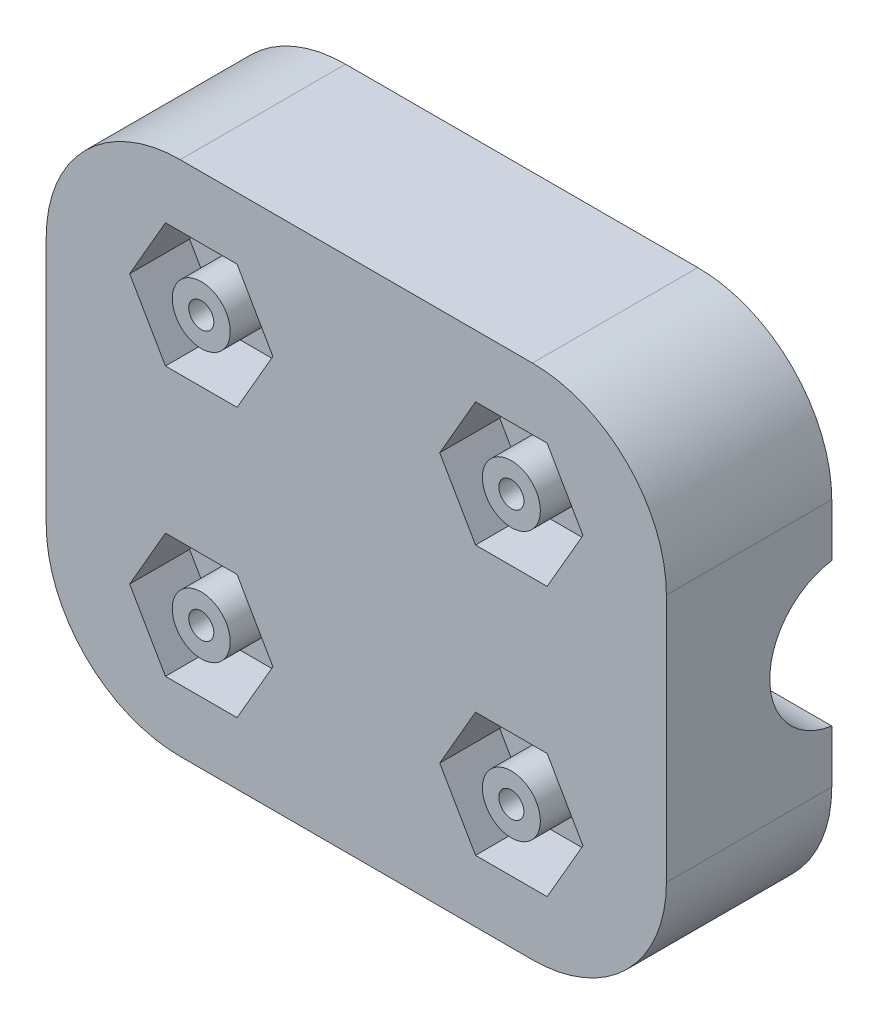
SolidWorks part; units mm, degrees
ref_plane "Front Plane" through (0, 0, 0) normal (0, 0, 1) x (1, 0, 0)
ref_plane "Top Plane" through (0, 0, 0) normal (0, 1, 0) x (1, 0, 0)
ref_plane "Right Plane" through (0, 0, 0) normal (1, 0, 0) x (0, 0, -1)
sketch "Sketch9" plane through (0, 0, 0) normal (0, 0, 1) x (1, 0, 0)
  line L1 (15, -20.0192) -> (15, -7.9808)
  line L3 (8.5192, -1.5) -> (-8.5192, -1.5)
  line L5 (-15, -7.9808) -> (-15, -20.0192)
  line L7 (-8.5192, -26.5) -> (8.5192, -26.5)
  arc A0 (15, -7.9808) -> (8.5192, -1.5) centre (8.5192, -7.9808) ccw
  arc A4 (-15, -20.0192) -> (-8.5192, -26.5) centre (-8.5192, -20.0192) ccw
  arc A5 (8.5192, -26.5) -> (15, -20.0192) centre (8.5192, -20.0192) ccw
  arc A6 (-8.5192, -1.5) -> (-15, -7.9808) centre (-8.5192, -7.9808) ccw
extrude "Boss-Extrude2" add sketch "Sketch9" against normal blind 8 separate body
sketch "Sketch10" plane through (0, 0, -8) normal (0, 0, -1) x (-1, 0, 0)
  line L0 (0, -1.5) -> (0, -26.5) construction
  line L1 (-8.5192, -1.5) -> (8.5192, -1.5) construction
  line L2 (8.5192, -26.5) -> (-8.5192, -26.5) construction
  line L4 (-15, -20.0192) -> (-15, -7.9808) construction
  line L5 (-15, -14) -> (15, -14) construction
  line L6 (15, -7.9808) -> (15, -20.0192) construction
  circle A0 centre (-7.5, -7.5) radius 1.8
  circle A1 centre (7.5, -7.5) radius 1.8
  circle A2 centre (7.5, -20.5) radius 1.8
  circle A3 centre (-7.5, -20.5) radius 1.8
extrude "Cut-Extrude5" cut sketch "Sketch10" against normal blind 4.7
sketch "Sketch11" plane through (0, 0, 0) normal (0, 0, 1) x (1, 0, 0)
  line L0 (0, -1.5) -> (0, -26.5) construction
  line L1 (8.5192, -1.5) -> (-8.5192, -1.5) construction
  line L2 (-8.5192, -26.5) -> (8.5192, -26.5) construction
  line L3 (9.2321, -4.5) -> (10.9641, -7.5)
  line L4 (-15, -7.9808) -> (-15, -20.0192) construction
  line L5 (-15, -14) -> (15, -14) construction
  line L6 (15, -20.0192) -> (15, -7.9808) construction
  line L7 (5.7679, -4.5) -> (9.2321, -4.5)
  line L8 (4.0359, -7.5) -> (5.7679, -4.5)
  line L9 (5.7679, -10.5) -> (4.0359, -7.5)
  line L10 (9.2321, -10.5) -> (5.7679, -10.5)
  line L11 (10.9641, -7.5) -> (9.2321, -10.5)
  line L12 (-9.2321, -23.5) -> (-10.9641, -20.5)
  line L13 (-5.7679, -23.5) -> (-9.2321, -23.5)
  line L14 (-4.0359, -20.5) -> (-5.7679, -23.5)
  line L15 (-5.7679, -17.5) -> (-4.0359, -20.5)
  line L16 (-9.2321, -17.5) -> (-5.7679, -17.5)
  line L17 (-10.9641, -20.5) -> (-9.2321, -17.5)
  line L18 (10.9641, -20.5) -> (9.2321, -17.5)
  line L19 (9.2321, -17.5) -> (5.7679, -17.5)
  line L20 (5.7679, -17.5) -> (4.0359, -20.5)
  line L21 (4.0359, -20.5) -> (5.7679, -23.5)
  line L22 (5.7679, -23.5) -> (9.2321, -23.5)
  line L23 (9.2321, -23.5) -> (10.9641, -20.5)
  line L73 (-10.9641, -7.5) -> (-9.2321, -10.5)
  line L74 (-9.2321, -10.5) -> (-5.7679, -10.5)
  line L75 (-5.7679, -10.5) -> (-4.0359, -7.5)
  line L76 (-4.0359, -7.5) -> (-5.7679, -4.5)
  line L77 (-5.7679, -4.5) -> (-9.2321, -4.5)
  line L78 (-9.2321, -4.5) -> (-10.9641, -7.5)
  circle A0 centre (-7.5, -7.5) radius 3 construction
  circle A1 centre (7.5, -7.5) radius 3 construction
  circle A2 centre (7.5, -20.5) radius 3 construction
  circle A3 centre (-7.5, -20.5) radius 3 construction
  dimension "D1" = 6
extrude "Cut-Extrude6" cut sketch "Sketch11" against normal blind 2.9
sketch "Sketch12" plane through (15, 0, 0) normal (1, 0, 0) x (0, 0, -1)
  circle A0 centre (8.5, -14) radius 3.5
extrude "Cut-Extrude7" cut sketch "Sketch12" against normal through all
sketch "Sketch13" plane through (-15, 0, 0) normal (-1, 0, 0) x (0, 0, 1)
  circle A0 centre (-8.5, -14) radius 4
extrude "Cut-Extrude8" cut sketch "Sketch13" against normal blind 15
sketch "Sketch14" plane through (0, 0, -2.9) normal (0, 0, 1) x (1, 0, 0)
  circle A8 centre (-7.5, -7.5) radius 1.4022
  circle A9 centre (7.5, -7.5) radius 1.4022
  circle A10 centre (-7.5, -20.5) radius 1.4022
  circle A11 centre (7.5, -20.5) radius 1.4022
  circle A12 centre (-7.5, -7.5) radius 0.6066
  circle A13 centre (7.5, -7.5) radius 0.6066
  circle A14 centre (7.5, -20.5) radius 0.6066
  circle A15 centre (-7.5, -20.5) radius 0.6066
  dimension "D5" = 0.7956
  dimension "D6" = 0.7956
  dimension "D7" = 0.7956
  dimension "D8" = 0.7956
extrude "Boss-Extrude3" add sketch "Sketch14" along normal up to surface (2.9 mm away) up to face at (-7.5, -7.5, 0)
